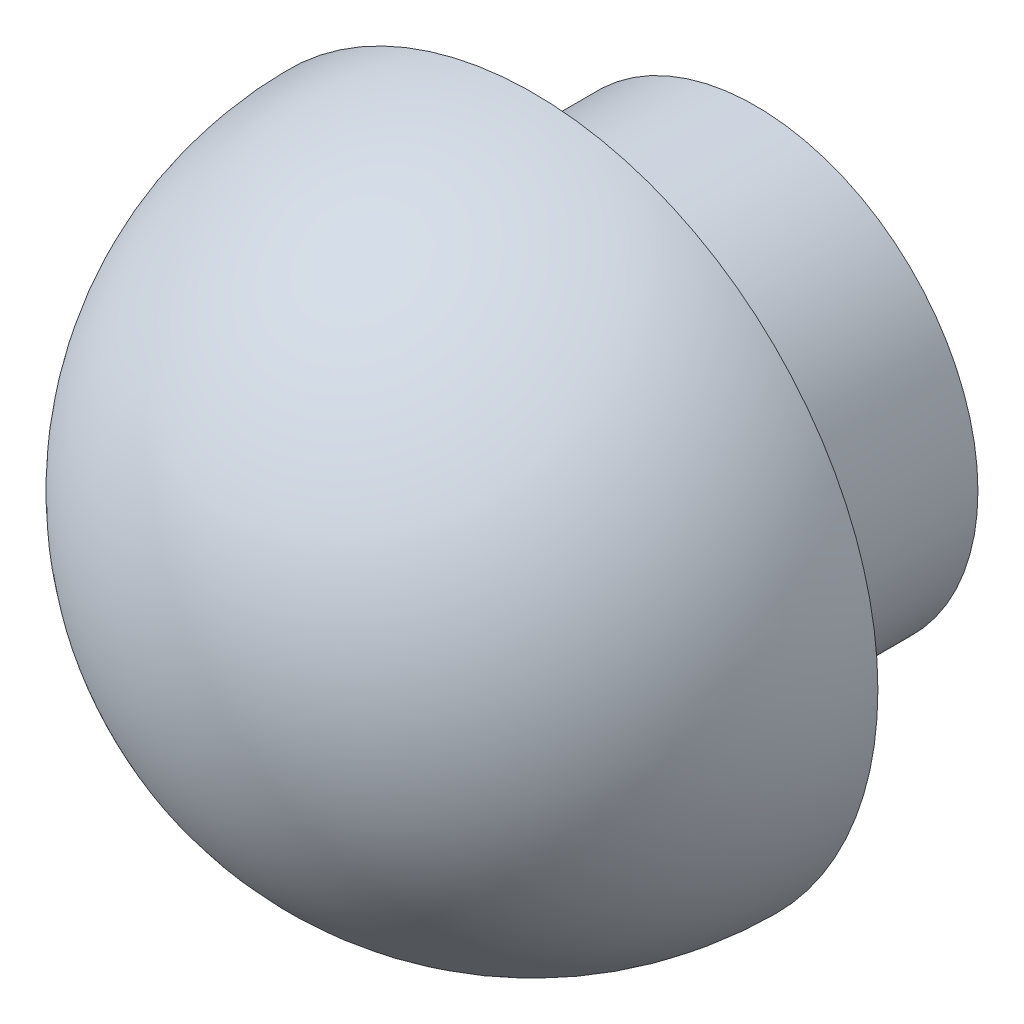
SolidWorks part; units mm, degrees
ref_plane "Front Plane" through (0, 0, 0) normal (0, 0, 1) x (1, 0, 0)
ref_plane "Top Plane" through (0, 0, 0) normal (0, 1, 0) x (1, 0, 0)
ref_plane "Right Plane" through (0, 0, 0) normal (1, 0, 0) x (0, 0, -1)
sketch "Sketch1" plane through (0, 0, 0) normal (0, 0, 1) x (1, 0, 0)
  circle A0 centre (0, 0) radius 15
  dimension "D1" = 30
extrude "Boss-Extrude1" add sketch "Sketch1" along normal blind 15
sketch "Sketch2" plane through (0, 0, 15) normal (0, 0, 1) x (1, 0, 0)
  line L0 (0, 0) -> (0, 23.25) construction
  line L1 (0, 0) -> (0, -23.25) construction
  line L2 (0, 23.25) -> (0, -23.25)
  arc A0 (0, 23.25) -> (0, -23.25) centre (0, 0) cw
  dimension "D3" = 23.25
  dimension "D1" = 23.25
  dimension "D2" = 23.25
revolve "Revolve1" add sketch "Sketch2" angle 180 about L0
